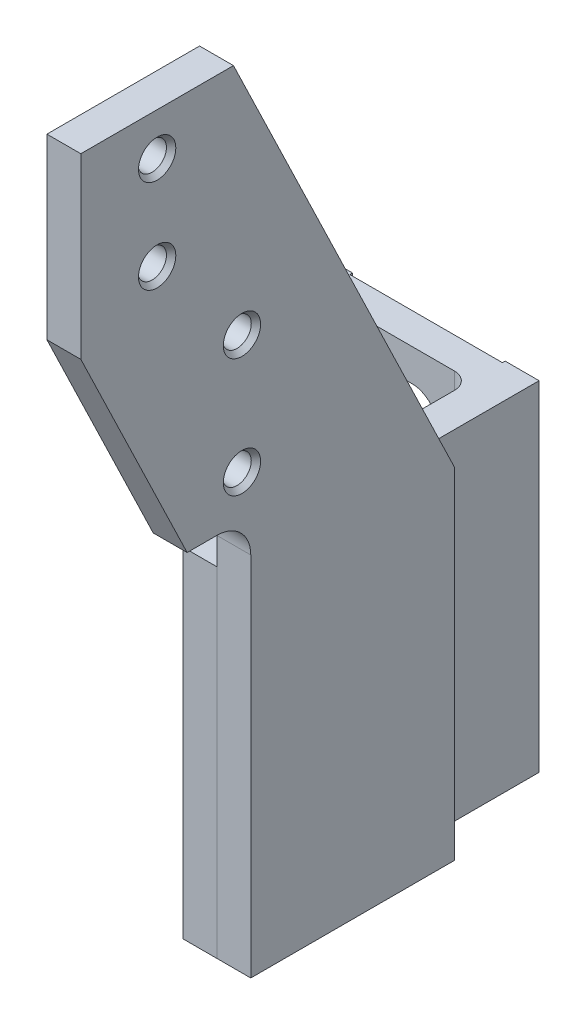
SolidWorks part; units mm, degrees
material "AISI 1018 Steel, Cold Rolled"
ref_plane "Front" through (0, 0, 0) normal (0, 0, 1) x (1, 0, 0)
ref_plane "Top" through (0, 0, 0) normal (0, 1, 0) x (1, 0, 0)
ref_plane "Right" through (0, 0, 0) normal (1, 0, 0) x (0, 0, -1)
sketch "Sketch1" plane through (0, 0, 0) normal (0, 0, 1) x (1, 0, 0)
  line L1 (0, 0) -> (-82.55, 0)
  line L2 (0, 0) -> (0, 127)
  line L3 (0, 127) -> (-82.55, 127)
  line L4 (-82.55, 0) -> (-82.55, 127)
  dimension "D1" = 127
  dimension "D2" = 82.55
extrude "Extrude1" add sketch "Sketch1" along normal blind 12.7
sketch "Sketch2" plane through (0, 0, 0) normal (0, 0, -1) x (-1, 0, 0)
  line L0 (0, 127) -> (82.55, 127) construction
  line L1 (12.7, 127) -> (69.85, 127)
  line L2 (12.7, 127) -> (12.7, 0)
  line L3 (12.7, 0) -> (69.85, 0)
  line L4 (69.85, 127) -> (69.85, 0)
  line L5 (82.55, 0) -> (0, 0) construction
  line L6 (0, 0) -> (0, 127) construction
  point P8 (41.275, 127)
  dimension "D1" = 12.7
extrude "Cut-Extrude1" cut sketch "Sketch2" against normal blind 1.016
sketch "Sketch3" plane through (0, 0, 12.7) normal (0, 0, 1) x (1, 0, 0)
  line L0 (-41.275, 114.935) -> (-41.275, 127) construction
  line L1 (-47.625, 114.935) -> (-34.925, 114.935)
  line L2 (0, 127) -> (-82.55, 127) construction
  line L3 (-47.625, 95.885) -> (-34.925, 95.885)
  line L4 (-41.275, 12.065) -> (-41.275, 0) construction
  line L5 (-47.625, 31.115) -> (-34.925, 31.115)
  line L6 (-82.55, 0) -> (0, 0) construction
  line L7 (-47.625, 12.065) -> (-34.925, 12.065)
  line L9 (-47.625, 76.835) -> (-34.925, 76.835)
  line L11 (-47.625, 57.785) -> (-34.925, 57.785)
  arc A0 (-47.625, 114.935) -> (-47.625, 95.885) centre (-47.625, 105.41) ccw
  arc A1 (-34.925, 95.885) -> (-34.925, 114.935) centre (-34.925, 105.41) ccw
  arc A2 (-34.925, 31.115) -> (-34.925, 12.065) centre (-34.925, 21.59) cw
  arc A3 (-47.625, 12.065) -> (-47.625, 31.115) centre (-47.625, 21.59) cw
  arc A4 (-47.625, 76.835) -> (-47.625, 57.785) centre (-47.625, 67.31) ccw
  arc A5 (-34.925, 57.785) -> (-34.925, 76.835) centre (-34.925, 67.31) ccw
  dimension "D1" = 83.82
  dimension "D2" = 19.05
  dimension "D3" = 12.7
  dimension "D4" = 38.1
extrude "Cut-Extrude2" cut sketch "Sketch3" against normal up to next
sketch "Sketch4" plane through (0, 0, 12.7) normal (0, 0, 1) x (1, 0, 0)
  line L0 (-82.55, 0) -> (0, 0) construction
  line L1 (0, 127) -> (-12.7, 127)
  line L2 (0, 127) -> (0, 0)
  line L3 (0, 0) -> (-12.7, 0)
  line L4 (-12.7, 127) -> (-12.7, 0)
  dimension "D1" = 12.7
extrude "Extrude3" add sketch "Sketch4" along normal offset from surface (107.95 mm away) 120.65 up to face at (-6.35, 63.5, 0)
sketch "Sketch5" plane through (0, 0, 0) normal (1, 0, 0) x (0, 0, -1)
  line L0 (-120.65, 0) -> (-44.45, 0)
  line L1 (-120.65, 0) -> (0, 0) construction
  line L2 (-44.45, 0) -> (-44.45, 299.085)
  line L3 (-44.45, 299.085) -> (-184.277, 299.085)
  line L4 (-184.277, 299.085) -> (-184.277, 149.86)
  line L5 (-184.277, 149.86) -> (-133.35, 149.86)
  line L6 (-120.65, 0) -> (-120.65, 137.16)
  line L7 (0, 0) -> (0, 127) construction
  arc A0 (-133.35, 149.86) -> (-120.65, 137.16) centre (-133.35, 137.16) cw
  dimension "D5" = 12.7
  dimension "D1" = 76.2
  dimension "D2" = 299.085
  dimension "D3" = 184.277
  dimension "D4" = 149.225
extrude "Extrude4" add sketch "Sketch5" along normal blind 12.7
sketch "Sketch6" plane through (12.7, 0, 0) normal (1, 0, 0) x (0, 0, -1)
  line L0 (-127.127, 299.085) -> (-44.45, 127.635)
  line L1 (-44.45, 299.085) -> (-184.277, 299.085) construction
  line L2 (-44.45, 0) -> (-44.45, 299.085) construction
  line L3 (-44.45, 127.635) -> (-44.45, 299.085)
  line L4 (-44.45, 299.085) -> (-127.127, 299.085)
  line L5 (-184.277, 299.085) -> (-184.277, 149.86) construction
  dimension "D1" = 57.15
  dimension "D2" = 171.45
extrude "Cut-Extrude3" cut sketch "Sketch6" against normal up to next
sketch "Sketch7" plane through (12.7, 0, 0) normal (1, 0, 0) x (0, 0, -1)
  line L0 (-184.277, 149.86) -> (-144.4696, 149.86)
  line L1 (-184.277, 149.86) -> (-133.35, 149.86) construction
  line L2 (-144.4696, 149.86) -> (-184.277, 232.41)
  line L3 (-184.277, 299.085) -> (-184.277, 149.86) construction
  line L4 (-184.277, 232.41) -> (-184.277, 149.86)
  line L5 (-127.127, 299.085) -> (-184.277, 299.085) construction
  line L6 (-127.127, 299.085) -> (-44.45, 127.635) construction
  dimension "D1" = 66.675
extrude "Cut-Extrude4" cut sketch "Sketch7" against normal through all
hole_wizard "1/2-13 Tapped Hole1" positions "Sketch9" profile "Sketch8" tap size "1/2-13" standard "Ansi Inch" end condition up to next
sketch "Sketch9" plane through (12.7, 0, 0) normal (1, 0, 0) x (0, 0, -1)
  line L0 (0, 0) -> (0, 127) construction
  line L1 (-1.016, 95.885) -> (-1.016, 114.935) construction
  point P0 (-155.702, 248.285)
  point P1 (-155.702, 283.21)
  point P7 (-1.016, 105.41)
  dimension "D1" = 155.702
  dimension "D2" = 142.875
  dimension "D3" = 34.925
sketch "Sketch8" plane through (12.7, 248.285, 155.702) normal (0, 1, 0) x (0, 0, -1)
  line L0 (0, 0) -> (0, 12.7)
  line L1 (0, 12.7) -> (6.985, 12.7)
  line L2 (5.3581, 10.8285) -> (5.3581, 1.8715)
  line L3 (5.3581, 1.8715) -> (6.985, 0)
  line L5 (6.985, 0) -> (0, 0)
  line L6 (-5.3581, 1.8715) -> (-6.985, 0) construction
  line L7 (6.985, 12.7) -> (5.3581, 10.8285)
  line L8 (-6.985, 12.7) -> (-5.3581, 10.8285) construction
  line L11 (0, -6.35) -> (0, 107.95) construction
  dimension "Thru Tap Drill Dia." = 10.7163
  dimension "Thru Tap Drill Depth" = 12.7
  dimension "Near C'Sink Dia." = 13.97
  dimension "Near C'Sink Angle" = 82
  dimension "Far C'Sink Dia." = 13.97
  dimension "Far C'Sink Angle" = 82
cosmetic thread "Hole Thread5" [suppressed] parameters "D2"=12.7
cosmetic thread "Hole Thread6" [suppressed] parameters "D2"=12.7
hole_wizard "1/2-13 Tapped Hole2" positions "Sketch11" profile "Sketch10" tap size "1/2-13" standard "Ansi Inch" end condition up to next
sketch "Sketch11" plane through (12.7, 0, 0) normal (1, 0, 0) x (0, 0, -1)
  line L0 (0, 0) -> (0, 127) construction
  line L1 (-144.4696, 149.86) -> (-133.35, 149.86) construction
  point P0 (-123.952, 210.185)
  point P1 (-123.952, 165.735)
  dimension "D1" = 123.952
  dimension "D2" = 15.875
  dimension "D3" = 44.45
sketch "Sketch10" plane through (12.7, 210.185, 123.952) normal (0, 1, 0) x (0, 0, -1)
  line L0 (0, 0) -> (0, 12.7)
  line L1 (0, 12.7) -> (6.985, 12.7)
  line L2 (5.3581, 10.8285) -> (5.3581, 1.8715)
  line L3 (5.3581, 1.8715) -> (6.985, 0)
  line L5 (6.985, 0) -> (0, 0)
  line L6 (-5.3581, 1.8715) -> (-6.985, 0) construction
  line L7 (6.985, 12.7) -> (5.3581, 10.8285)
  line L8 (-6.985, 12.7) -> (-5.3581, 10.8285) construction
  line L11 (0, -6.35) -> (0, 107.95) construction
  dimension "Thru Tap Drill Dia." = 10.7163
  dimension "Thru Tap Drill Depth" = 12.7
  dimension "Near C'Sink Dia." = 13.97
  dimension "Near C'Sink Angle" = 82
  dimension "Far C'Sink Dia." = 13.97
  dimension "Far C'Sink Angle" = 82
cosmetic thread "Hole Thread3" [suppressed] parameters "D2"=12.7
cosmetic thread "Hole Thread4" [suppressed] parameters "D2"=12.7
fillet "Fillet1" radius 6.35 1 edges
sketch "Sketch12" [suppressed] plane through (0, 0, 12.7) normal (0, 0, 1) x (1, 0, 0)
  line L0 (-82.55, 0) -> (0, 0) construction
  line L1 (-82.55, 127) -> (-69.85, 127)
  line L2 (-82.55, 127) -> (-82.55, 0)
  line L3 (-82.55, 0) -> (-69.85, 0)
  line L4 (-69.85, 127) -> (-69.85, 0)
  dimension "D1" = 12.7
extrude "Extrude5" [suppressed] add sketch "Sketch12" along normal offset from surface (107.95 mm away) 120.65
sketch "Sketch13" [suppressed] plane through (-82.55, 0, 0) normal (-1, 0, 0) x (0, 0, 1)
  line L0 (44.45, 0) -> (120.65, 0)
  line L1 (120.65, 0) -> (0, 0) construction
  line L2 (120.65, 0) -> (120.65, 137.16)
  line L3 (133.35, 149.86) -> (184.277, 149.86)
  line L4 (184.277, 149.86) -> (184.277, 299.085)
  line L5 (184.277, 299.085) -> (44.45, 299.085)
  line L6 (44.45, 299.085) -> (44.45, 0)
  line L7 (0, 127) -> (0, 0) construction
  arc A0 (120.65, 137.16) -> (133.35, 149.86) centre (133.35, 137.16) cw
  dimension "D5" = 12.7
  dimension "D1" = 76.2
  dimension "D2" = 184.277
  dimension "D3" = 299.085
  dimension "D4" = 149.225
extrude "Extrude6" [suppressed] add sketch "Sketch13" along normal blind 12.7
sketch "Sketch14" [suppressed] plane through (-95.25, 0, 0) normal (-1, 0, 0) x (0, 0, 1)
  line L0 (44.45, 127.635) -> (127.127, 299.085)
  line L1 (44.45, 299.085) -> (44.45, 0) construction
  line L2 (184.277, 299.085) -> (44.45, 299.085) construction
  line L3 (127.127, 299.085) -> (44.45, 299.085)
  line L4 (44.45, 299.085) -> (44.45, 127.635)
  line L5 (184.277, 149.86) -> (184.277, 299.085) construction
  dimension "D1" = 171.45
  dimension "D2" = 57.15
extrude "Cut-Extrude5" [suppressed] cut sketch "Sketch14" against normal up to next
sketch "Sketch15" [suppressed] plane through (-95.25, 0, 0) normal (-1, 0, 0) x (0, 0, 1)
  line L0 (144.4696, 149.86) -> (184.277, 149.86)
  line L1 (133.35, 149.86) -> (184.277, 149.86) construction
  line L2 (184.277, 149.86) -> (184.277, 232.41)
  line L3 (184.277, 149.86) -> (184.277, 299.085) construction
  line L4 (184.277, 232.41) -> (144.4696, 149.86)
  line L5 (184.277, 299.085) -> (127.127, 299.085) construction
  line L6 (44.45, 127.635) -> (127.127, 299.085) construction
  dimension "D1" = 66.675
extrude "Cut-Extrude6" [suppressed] cut sketch "Sketch15" against normal up to next
hole_wizard "1/2-13 Tapped Hole3" positions "Sketch17" profile "Sketch16" tap size "1/2-13" standard "Ansi Inch" end condition up to next
sketch "Sketch17" plane through (-95.25, 0, 0) normal (-1, 0, 0) x (0, 0, 1)
  line L0 (0, 127) -> (0, 0) construction
  line L1 (1.016, 114.935) -> (1.016, 95.885) construction
  point P0 (155.702, 283.21)
  point P1 (155.702, 248.285)
  point P6 (1.016, 105.41)
  dimension "D1" = 155.702
  dimension "D2" = 34.925
  dimension "D3" = 142.875
sketch "Sketch16" plane through (-95.25, 283.21, 155.702) normal (0, 1, 0) x (0, 0, 1)
  line L0 (0, 0) -> (0, 12.7)
  line L1 (0, 12.7) -> (6.985, 12.7)
  line L2 (5.3581, 10.8285) -> (5.3581, 1.8715)
  line L3 (5.3581, 1.8715) -> (6.985, 0)
  line L5 (6.985, 0) -> (0, 0)
  line L6 (-5.3581, 1.8715) -> (-6.985, 0) construction
  line L7 (6.985, 12.7) -> (5.3581, 10.8285)
  line L8 (-6.985, 12.7) -> (-5.3581, 10.8285) construction
  line L11 (0, -6.35) -> (0, 107.95) construction
  dimension "Thru Tap Drill Dia." = 10.7163
  dimension "Thru Tap Drill Depth" = 12.7
  dimension "Near C'Sink Dia." = 13.97
  dimension "Near C'Sink Angle" = 82
  dimension "Far C'Sink Dia." = 13.97
  dimension "Far C'Sink Angle" = 82
cosmetic thread "Hole Thread7" [suppressed] parameters "D2"=12.7
cosmetic thread "Hole Thread8" [suppressed] parameters "D2"=12.7
hole_wizard "1/2-13 Tapped Hole4" positions "Sketch19" profile "Sketch18" tap size "1/2-13" standard "Ansi Inch" end condition up to next
sketch "Sketch19" plane through (-95.25, 0, 0) normal (-1, 0, 0) x (0, 0, 1)
  line L0 (133.35, 149.86) -> (144.4696, 149.86) construction
  line L1 (0, 127) -> (0, 0) construction
  point P0 (123.952, 210.185)
  point P1 (123.952, 165.735)
  dimension "D1" = 15.875
  dimension "D2" = 44.45
  dimension "D3" = 123.952
sketch "Sketch18" plane through (-95.25, 210.185, 123.952) normal (0, 1, 0) x (0, 0, 1)
  line L0 (0, 0) -> (0, 12.7)
  line L1 (0, 12.7) -> (6.985, 12.7)
  line L2 (5.3581, 10.8285) -> (5.3581, 1.8715)
  line L3 (5.3581, 1.8715) -> (6.985, 0)
  line L5 (6.985, 0) -> (0, 0)
  line L6 (-5.3581, 1.8715) -> (-6.985, 0) construction
  line L7 (6.985, 12.7) -> (5.3581, 10.8285)
  line L8 (-6.985, 12.7) -> (-5.3581, 10.8285) construction
  line L11 (0, -6.35) -> (0, 107.95) construction
  dimension "Thru Tap Drill Dia." = 10.7163
  dimension "Thru Tap Drill Depth" = 12.7
  dimension "Near C'Sink Dia." = 13.97
  dimension "Near C'Sink Angle" = 82
  dimension "Far C'Sink Dia." = 13.97
  dimension "Far C'Sink Angle" = 82
cosmetic thread "Hole Thread9" [suppressed] parameters "D2"=12.7
cosmetic thread "Hole Thread10" [suppressed] parameters "D2"=12.7
fillet "Fillet2" [suppressed] radius 6.35
sketch "Sketch20" plane through (0, 0, 120.65) normal (0, 0, 1) x (1, 0, 0)
  line L0 (-12.7, 0) -> (12.7, 0) construction
  line L1 (-12.7, 127) -> (0, 127)
  line L2 (-12.7, 127) -> (-12.7, 0)
  line L3 (-12.7, 0) -> (0, 0)
  line L4 (0, 127) -> (0, 0)
  line L5 (0, 137.16) -> (0, 127) construction
split line "Split Line1"
sketch "Sketch21" plane through (0, 0, 0) normal (0, -1, 0) x (1, 0, 0)
  line L1 (0, 44.45) -> (12.7, 44.45)
  line L2 (0, 44.45) -> (0, 120.65)
  line L3 (0, 120.65) -> (12.7, 120.65)
  line L4 (12.7, 44.45) -> (12.7, 120.65)
split line "Split Line2"
sketch "Sketch22" [suppressed] plane through (0, 0, 120.65) normal (0, 0, 1) x (1, 0, 0)
  line L1 (-82.55, 127) -> (-69.85, 127)
  line L2 (-82.55, 127) -> (-82.55, 0)
  line L3 (-82.55, 0) -> (-69.85, 0)
  line L4 (-69.85, 127) -> (-69.85, 0)
split line "Split Line3" [suppressed]
sketch "Sketch23" [suppressed] plane through (0, 0, 0) normal (0, -1, 0) x (1, 0, 0)
  line L1 (-82.55, 44.45) -> (-95.25, 44.45)
  line L2 (-82.55, 44.45) -> (-82.55, 120.65)
  line L3 (-82.55, 120.65) -> (-95.25, 120.65)
  line L4 (-95.25, 44.45) -> (-95.25, 120.65)
split line "Split Line4" [suppressed]
